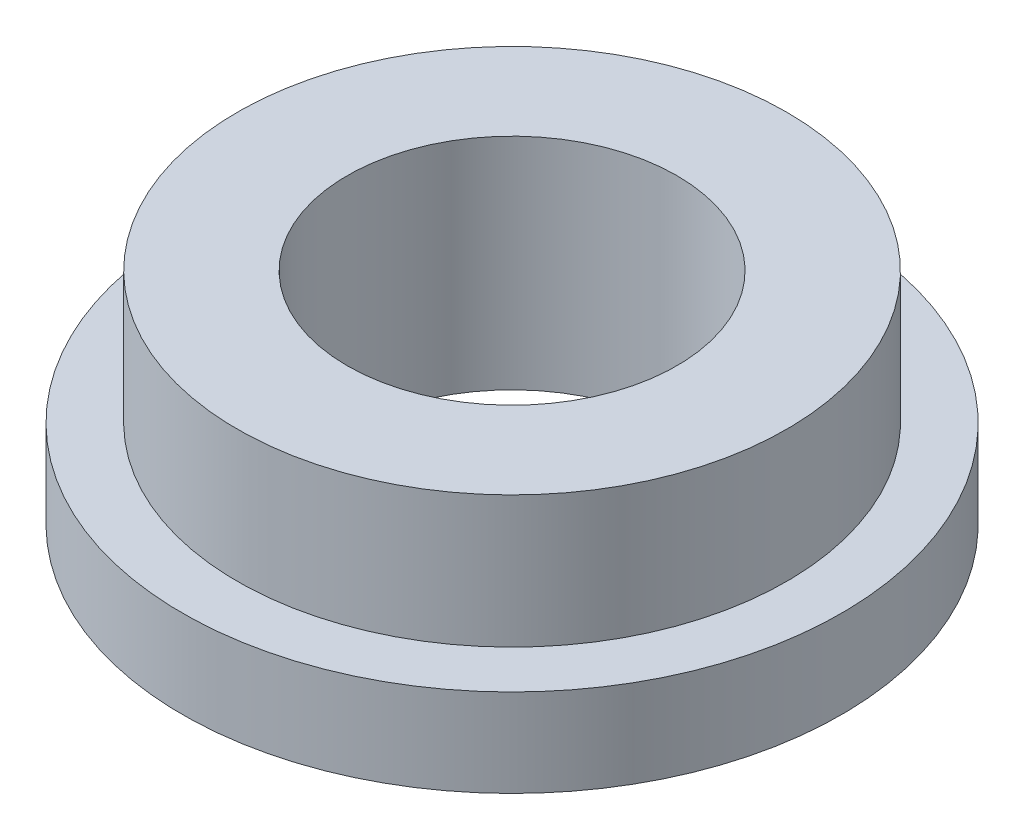
SolidWorks part; units mm, degrees
ref_plane "Plan de face" through (0, 0, 0) normal (0, 0, 1) x (1, 0, 0)
ref_plane "Plan de dessus" through (0, 0, 0) normal (0, 1, 0) x (1, 0, 0)
ref_plane "Plan de droite" through (0, 0, 0) normal (1, 0, 0) x (0, 0, -1)
sketch "Esquisse1" plane through (0, 0, 0) normal (1, 0, 0) x (0, 0, -1)
  line L0 (0, -11.7) -> (0, 14.8286) construction
  line L2 (3, 0) -> (3, 4)
  line L3 (3, 4) -> (5, 4)
  line L4 (5, 4) -> (5, 1.6)
  line L5 (5, 1.6) -> (6, 1.6)
  line L6 (6, 1.6) -> (6, 0)
  line L7 (6, 0) -> (3, 0)
  dimension "D1" = 3
  dimension "D2" = 5
  dimension "D3" = 6
  dimension "D4" = 4
  dimension "D5" = 1.6
revolve "Révolution1" add sketch "Esquisse1" angle 360 about L0
